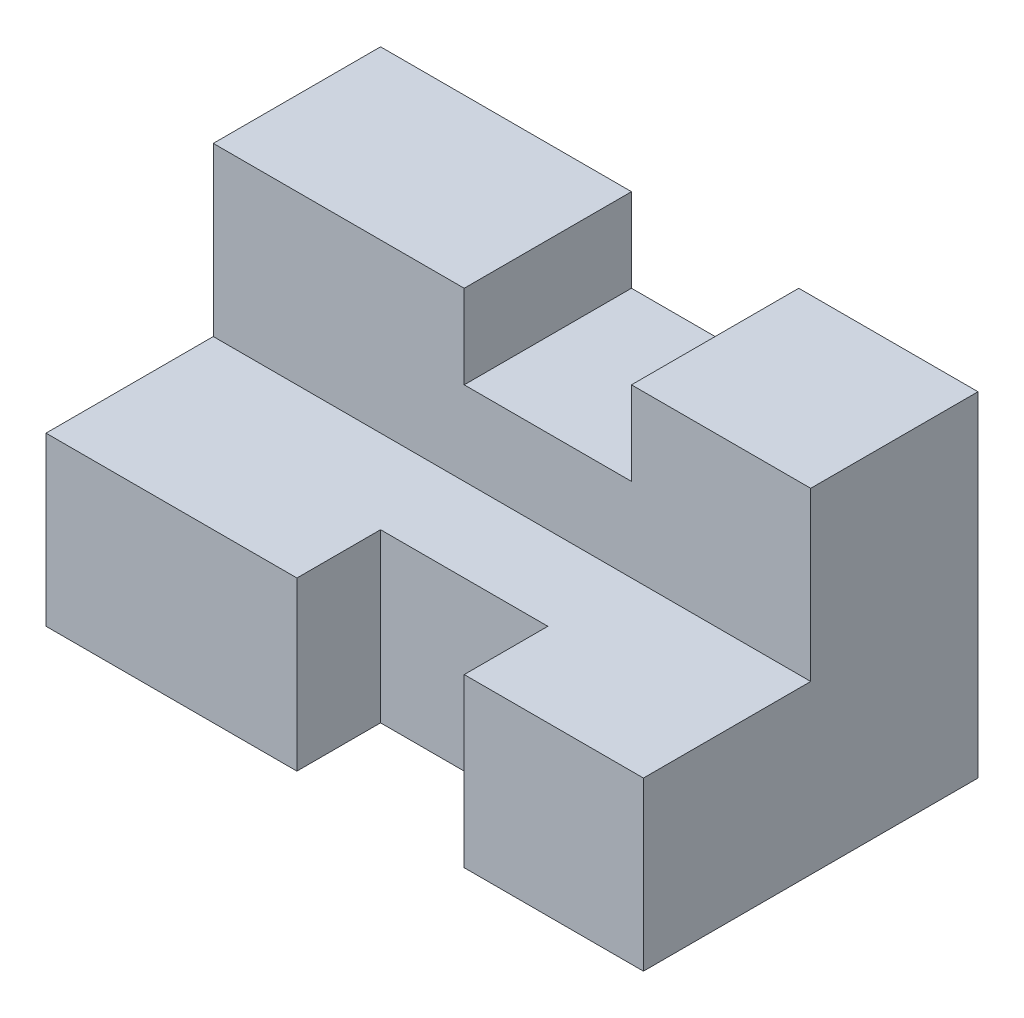
SolidWorks part; units mm, degrees
ref_plane "Front Plane" through (0, 0, 0) normal (0, 0, 1) x (1, 0, 0)
ref_plane "Top Plane" through (0, 0, 0) normal (0, 1, 0) x (1, 0, 0)
ref_plane "Right Plane" through (0, 0, 0) normal (1, 0, 0) x (0, 0, -1)
sketch "Sketch2" plane through (0, 0, 0) normal (1, 0, 0) x (0, 0, -1)
  line L0 (0, 0) -> (-28, 0)
  line L1 (-28, 0) -> (-28, 14)
  line L2 (-28, 14) -> (-14, 14)
  line L3 (-14, 14) -> (0, 0)
  dimension "D1" = 28
  dimension "D2" = 14
  dimension "D3" = 14
extrude "Boss-Extrude1" add sketch "Sketch2" along normal mid plane 50
sketch "Sketch3" plane through (0, 14, 0) normal (0, 1, 0) x (1, 0, 0)
  line L0 (-4, -28) -> (-4, -21)
  line L1 (-4, -21) -> (10, -21)
  line L2 (10, -21) -> (10, -28)
  line L4 (-25, -14) -> (-25, -28)
  line L5 (-25, -28) -> (25, -28)
  line L6 (25, -28) -> (25, -14)
  line L7 (25, -14) -> (-25, -14)
  line L8 (-25, -14) -> (-25, -28)
  line L9 (-25, -28) -> (25, -28)
  line L10 (25, -28) -> (25, -14)
  line L11 (25, -14) -> (-25, -14)
  line M6 (-25, -28) -> (25, -28)
  dimension "D2" = 7
  dimension "D3" = 21
  dimension "D4" = 14
  dimension "D1" = 0
extrude "Cut-Extrude1" cut sketch "Sketch3" against normal up to next contours L2 L1 L0 M6
mirror "Mirror1" about plane through (25, 14, 14) normal (0, -0.7071, 0.7071) of bodies 102
